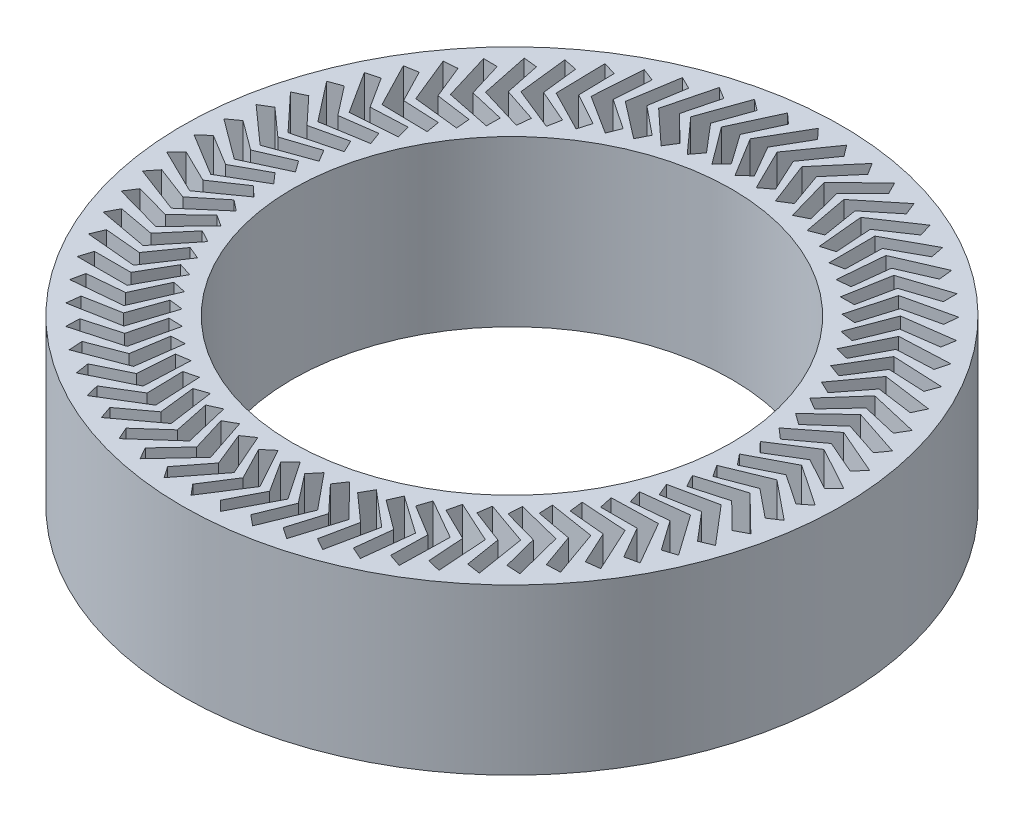
SolidWorks part; units mm, degrees
material "BUTYL"
ref_plane "Front Plane" through (0, 0, 0) normal (0, 0, 1) x (1, 0, 0)
ref_plane "Top Plane" through (0, 0, 0) normal (0, 1, 0) x (1, 0, 0)
ref_plane "Right Plane" through (0, 0, 0) normal (1, 0, 0) x (0, 0, -1)
sketch "Sketch1" plane through (0, 0, 0) normal (0, 1, 0) x (1, 0, 0)
  circle A0 centre (0, 0) radius 152.4
  circle A1 centre (0, 0) radius 101.6
  dimension "D1" = 304.8
  dimension "D2" = 203.2
extrude "Boss-Extrude1" add sketch "Sketch1" along normal blind 76.2
sketch "Sketch2" plane through (0, 76.2, 0) normal (0, 1, 0) x (1, 0, 0)
  line L0 (0, 0) -> (0, 152.4) construction
  line L1 (0, 141.3041) -> (-4.2887, 145.987)
  line L2 (-4.2887, 145.987) -> (-15.8221, 126.0106)
  line L3 (-15.8221, 126.0106) -> (-4.6829, 107.8484)
  line L4 (-4.6829, 107.8484) -> (0, 112.1371)
  line L5 (0, 141.3041) -> (-8.4198, 126.7206)
  line L6 (-8.4198, 126.7206) -> (0, 112.1371)
  line L7 (3.1384, 126.9612) -> (10.1972, 111.6725)
  line L8 (5.1437, 107.8274) -> (10.1972, 111.6725)
  line L9 (-4.2978, 126.9273) -> (5.1437, 107.8274)
  line L10 (9.0044, 145.7722) -> (-4.2978, 126.9273)
  line L11 (12.8495, 140.7187) -> (9.0044, 145.7722)
  line L12 (12.8495, 140.7187) -> (3.1384, 126.9612)
  line L13 (14.6706, 126.1498) -> (20.3098, 110.2825)
  line L14 (14.9276, 106.9129) -> (20.3098, 110.2825)
  line L15 (7.2621, 126.7922) -> (14.9276, 106.9129)
  line L16 (22.2229, 144.3494) -> (7.2621, 126.7922)
  line L17 (25.5925, 138.9672) -> (22.2229, 144.3494)
  line L18 (25.5925, 138.9672) -> (14.6706, 126.1498)
  line L19 (26.0812, 124.2931) -> (30.2542, 107.9787)
  line L20 (24.5879, 105.1125) -> (30.2542, 107.9787)
  line L21 (18.7619, 125.6065) -> (24.5879, 105.1125)
  line L22 (35.2572, 141.7305) -> (18.7619, 125.6065)
  line L23 (38.1234, 136.0642) -> (35.2572, 141.7305)
  line L24 (38.1234, 136.0642) -> (26.0812, 124.2931)
  line L25 (37.2757, 121.4064) -> (39.9479, 104.7802)
  line L26 (34.0444, 102.4411) -> (39.9479, 104.7802)
  line L27 (30.1061, 123.38) -> (34.0444, 102.4411)
  line L28 (47.9993, 137.9372) -> (30.1061, 123.38)
  line L29 (50.3384, 132.0337) -> (47.9993, 137.9372)
  line L30 (50.3384, 132.0337) -> (37.2757, 121.4064)
  line L31 (48.1614, 117.5137) -> (49.3106, 100.7134)
  line L32 (43.2188, 98.9209) -> (49.3106, 100.7134)
  line L33 (41.201, 120.1311) -> (43.2188, 98.9209)
  line L34 (60.3438, 133.0009) -> (41.201, 120.1311)
  line L35 (62.1363, 126.9091) -> (60.3438, 133.0009)
  line L36 (62.1363, 126.9091) -> (48.1614, 117.5137)
  line L37 (58.6479, 112.6473) -> (58.2646, 95.8121)
  line L38 (52.0351, 94.5809) -> (58.2646, 95.8121)
  line L39 (51.9544, 115.8868) -> (52.0351, 94.5809)
  line L40 (72.1882, 126.9625) -> (51.9544, 115.8868)
  line L41 (73.4193, 120.733) -> (72.1882, 126.9625)
  line L42 (73.4193, 120.733) -> (58.6479, 112.6473)
  line L43 (68.6485, 106.8475) -> (66.7359, 90.1168)
  line L44 (60.4202, 89.4572) -> (66.7359, 90.1168)
  line L45 (62.2772, 110.6822) -> (60.4202, 89.4572)
  line L46 (83.4344, 119.872) -> (62.2772, 110.6822)
  line L47 (84.094, 113.5564) -> (83.4344, 119.872)
  line L48 (84.094, 113.5564) -> (68.6485, 106.8475)
  line L49 (78.0803, 100.1622) -> (74.6541, 83.6748)
  line L50 (68.3047, 83.5923) -> (74.6541, 83.6748)
  line L51 (72.0841, 104.5604) -> (68.3047, 83.5923)
  line L52 (93.9893, 111.7883) -> (72.0841, 104.5604)
  line L53 (94.0718, 105.4388) -> (93.9893, 111.7883)
  line L54 (94.0718, 105.4388) -> (78.0803, 100.1622)
  line L55 (86.865, 92.647) -> (81.9538, 76.5395)
  line L56 (75.6231, 77.0347) -> (81.9538, 76.5395)
  line L57 (81.2936, 97.5723) -> (75.6231, 77.0347)
  line L58 (103.7653, 102.7782) -> (81.2936, 97.5723)
  line L59 (103.2701, 96.4476) -> (103.7653, 102.7782)
  line L60 (103.2701, 96.4476) -> (86.865, 92.647)
  line L61 (94.93, 84.3641) -> (88.5744, 68.7699)
  line L62 (82.315, 69.8387) -> (88.5744, 68.7699)
  line L63 (89.8295, 89.7756) -> (82.315, 69.8387)
  line L64 (112.6815, 92.9165) -> (89.8295, 89.7756)
  line L65 (111.6127, 86.6571) -> (112.6815, 92.9165)
  line L66 (111.6127, 86.6571) -> (94.93, 84.3641)
  line L67 (102.2083, 75.3821) -> (94.461, 60.4305)
  line L68 (88.3247, 62.0641) -> (94.461, 60.4305)
  line L69 (97.6211, 81.235) -> (88.3247, 62.0641)
  line L70 (120.664, 82.2849) -> (97.6211, 81.235)
  line L71 (119.0304, 76.1486) -> (120.664, 82.2849)
  line L72 (119.0304, 76.1486) -> (102.2083, 75.3821)
  line L73 (108.6397, 65.7755) -> (99.5648, 51.5903)
  line L74 (93.6025, 53.7752) -> (99.5648, 51.5903)
  line L75 (104.6037, 72.0213) -> (93.6025, 53.7752)
  line L76 (127.6466, 70.9714) -> (104.6037, 72.0213)
  line L77 (125.4618, 65.0091) -> (127.6466, 70.9714)
  line L78 (125.4618, 65.0091) -> (108.6397, 65.7755)
  line L79 (114.1709, 55.6239) -> (103.8437, 42.3227)
  line L80 (98.1048, 45.0406) -> (103.8437, 42.3227)
  line L81 (110.7196, 62.2107) -> (98.1048, 45.0406)
  line L82 (133.5716, 59.0698) -> (110.7196, 62.2107)
  line L83 (130.8536, 53.3309) -> (133.5716, 59.0698)
  line L84 (130.8536, 53.3309) -> (114.1709, 55.6239)
  line L85 (118.756, 45.0113) -> (107.2621, 32.7043)
  line L86 (101.7941, 35.9329) -> (107.2621, 32.7043)
  line L87 (115.918, 51.8847) -> (101.7941, 35.9329)
  line L88 (138.3897, 46.6788) -> (115.918, 51.8847)
  line L89 (135.1611, 41.2108) -> (138.3897, 46.6788)
  line L90 (135.1611, 41.2108) -> (118.756, 45.0113)
  line L91 (122.3571, 34.0258) -> (109.7916, 22.815)
  line L92 (104.6399, 26.5274) -> (109.7916, 22.815)
  line L93 (120.1558, 41.1288) -> (104.6399, 26.5274)
  line L94 (142.061, 33.9009) -> (120.1558, 41.1288)
  line L95 (138.3486, 28.7492) -> (142.061, 33.9009)
  line L96 (138.3486, 28.7492) -> (122.3571, 34.0258)
  line L97 (124.9442, 22.7583) -> (111.4114, 12.7365)
  line L98 (106.6186, 16.902) -> (111.4114, 12.7365)
  line L99 (123.398, 30.032) -> (106.6186, 16.902)
  line L100 (144.5552, 20.8422) -> (123.398, 30.032)
  line L101 (140.3897, 16.0493) -> (144.5552, 20.8422)
  line L102 (140.3897, 16.0493) -> (124.9442, 22.7583)
  line L103 (126.4961, 11.3022) -> (112.108, 2.5526)
  line L104 (107.7138, 7.1367) -> (112.108, 2.5526)
  line L105 (125.6177, 18.6864) -> (107.7138, 7.1367)
  line L106 (145.8516, 7.6107) -> (125.6177, 18.6864)
  line L107 (141.2675, 3.2165) -> (145.8516, 7.6107)
  line L108 (141.2675, 3.2165) -> (126.4961, 11.3022)
  line L109 (126.9998, -0.2475) -> (111.8756, -7.6525)
  line L110 (107.9165, -2.6878) -> (111.8756, -7.6525)
  line L111 (126.7965, 7.186) -> (107.9165, -2.6878)
  line L112 (145.9394, -5.6838) -> (126.7965, 7.186)
  line L113 (140.9747, -9.6429) -> (145.9394, -5.6838)
  line L114 (140.9747, -9.6429) -> (126.9998, -0.2475)
  line L115 (126.4511, -11.7952) -> (110.7163, -17.7942)
  line L116 (107.225, -12.4901) -> (110.7163, -17.7942)
  line L117 (126.9247, -4.374) -> (107.225, -12.4901)
  line L118 (144.8179, -18.9312) -> (126.9247, -4.374)
  line L119 (139.5137, -22.4225) -> (144.8179, -18.9312)
  line L120 (139.5137, -22.4225) -> (126.4511, -11.7952)
  line L121 (124.8546, -23.2452) -> (108.6394, -27.7884)
  line L122 (105.645, -22.1888) -> (108.6394, -27.7884)
  line L123 (126.001, -15.8978) -> (105.645, -22.1888)
  line L124 (142.4963, -32.0218) -> (126.001, -15.8978)
  line L125 (136.8967, -35.0163) -> (142.4963, -32.0218)
  line L126 (136.8967, -35.0163) -> (124.8546, -23.2452)
  line L127 (122.2235, -34.5025) -> (105.6624, -37.5524)
  line L128 (103.1895, -31.7037) -> (105.6624, -37.5524)
  line L129 (124.0333, -27.2898) -> (103.1895, -31.7037)
  line L130 (138.9941, -44.847) -> (124.0333, -27.2898)
  line L131 (133.1453, -47.3199) -> (138.9941, -44.847)
  line L132 (133.1453, -47.3199) -> (122.2235, -34.5025)
  line L133 (118.5796, -45.4739) -> (101.8098, -47.0052)
  line L134 (99.879, -40.9559) -> (101.8098, -47.0052)
  line L135 (121.0378, -38.4557) -> (99.879, -40.9559)
  line L136 (134.34, -57.3006) -> (121.0378, -38.4557)
  line L137 (128.2907, -59.2314) -> (134.34, -57.3006)
  line L138 (128.2907, -59.2314) -> (118.5796, -45.4739)
  line L139 (113.9531, -56.0685) -> (97.1135, -56.0685)
  line L140 (95.7409, -49.8687) -> (97.1135, -56.0685)
  line L141 (117.0394, -49.3029) -> (95.7409, -49.8687)
  line L142 (128.5728, -69.2794) -> (117.0394, -49.3029)
  line L143 (122.3729, -70.6521) -> (128.5728, -69.2794)
  line L144 (122.3729, -70.6521) -> (113.9531, -56.0685)
  line L145 (108.3824, -66.1985) -> (91.6126, -64.6672)
  line L146 (90.8094, -58.3682) -> (91.6126, -64.6672)
  line L147 (112.0711, -59.7416) -> (90.8094, -58.3682)
  line L148 (121.7402, -80.6841) -> (112.0711, -59.7416)
  line L149 (115.4412, -81.4873) -> (121.7402, -80.6841)
  line L150 (115.4412, -81.4873) -> (108.3824, -66.1985)
  line L151 (101.9136, -75.78) -> (85.3525, -72.7301)
  line L152 (85.1255, -66.3842) -> (85.3525, -72.7301)
  line L153 (106.1742, -69.6853) -> (85.1255, -66.3842)
  line L154 (113.8988, -91.4203) -> (106.1742, -69.6853)
  line L155 (107.5529, -91.6473) -> (113.8988, -91.4203)
  line L156 (107.5529, -91.6473) -> (101.9136, -75.78)
  line L157 (94.6003, -84.7336) -> (78.3852, -80.1903)
  line L158 (78.7362, -73.85) -> (78.3852, -80.1903)
  line L159 (99.3975, -79.0515) -> (78.7362, -73.85)
  line L160 (105.1136, -101.3989) -> (99.3975, -79.0515)
  line L161 (98.7733, -101.0479) -> (105.1136, -101.3989)
  line L162 (98.7733, -101.0479) -> (94.6003, -84.7336)
  line L163 (86.5032, -92.985) -> (70.7684, -86.986)
  line L164 (71.6944, -80.7039) -> (70.7684, -86.986)
  line L165 (91.7971, -87.7627) -> (71.6944, -80.7039)
  line L166 (95.4574, -110.5372) -> (91.7971, -87.7627)
  line L167 (89.1753, -109.6112) -> (95.4574, -110.5372)
  line L168 (89.1753, -109.6112) -> (86.5032, -92.985)
  line L169 (77.6892, -100.4659) -> (62.5651, -93.0609)
  line L170 (64.0586, -86.889) -> (62.5651, -93.0609)
  line L171 (83.4361, -95.7466) -> (64.0586, -86.889)
  line L172 (85.0102, -118.7597) -> (83.4361, -95.7466)
  line L173 (78.8384, -117.2662) -> (85.0102, -118.7597)
  line L174 (78.8384, -117.2662) -> (77.6892, -100.4659)
  line L175 (68.2315, -107.1143) -> (53.8434, -98.3647)
  line L176 (55.8919, -92.3542) -> (53.8434, -98.3647)
  line L177 (74.3837, -102.9372) -> (55.8919, -92.3542)
  line L178 (73.8586, -125.998) -> (74.3837, -102.9372)
  line L179 (67.8481, -123.9495) -> (73.8586, -125.998)
  line L180 (67.8481, -123.9495) -> (68.2315, -107.1143)
  line L181 (58.2084, -112.8751) -> (44.6755, -102.8534)
  line L182 (47.2621, -97.0541) -> (44.6755, -102.8534)
  line L183 (64.715, -109.2748) -> (47.2621, -97.0541)
  line L184 (62.095, -132.1923) -> (64.715, -109.2748)
  line L185 (56.2957, -129.6057) -> (62.095, -132.1923)
  line L186 (56.2957, -129.6057) -> (58.2084, -112.8751)
  line L187 (47.7029, -117.7006) -> (35.1375, -106.4898)
  line L188 (38.2407, -100.9497) -> (35.1375, -106.4898)
  line L189 (54.5099, -114.7069) -> (38.2407, -100.9497)
  line L190 (49.8169, -137.2912) -> (54.5099, -114.7069)
  line L191 (44.2768, -134.188) -> (49.8169, -137.2912)
  line L192 (44.2768, -134.188) -> (47.7029, -117.7006)
  line L193 (36.8022, -121.5508) -> (25.3083, -109.2438)
  line L194 (28.9024, -104.0089) -> (25.3083, -109.2438)
  line L195 (43.8532, -119.1885) -> (28.9024, -104.0089)
  line L196 (37.1259, -141.2525) -> (43.8532, -119.1885)
  line L197 (31.891, -137.6583) -> (37.1259, -141.2525)
  line L198 (31.891, -137.6583) -> (36.8022, -121.5508)
  line L199 (25.5965, -124.3938) -> (15.2693, -111.0926)
  line L200 (19.3246, -106.2062) -> (15.2693, -111.0926)
  line L201 (32.8332, -122.6824) -> (19.3246, -106.2062)
  line L202 (24.1273, -144.0433) -> (32.8332, -122.6824)
  line L203 (19.2409, -139.988) -> (24.1273, -144.0433)
  line L204 (19.2409, -139.988) -> (25.5965, -124.3938)
  line L205 (14.1787, -126.206) -> (5.1039, -112.0209)
  line L206 (9.5867, -107.5235) -> (5.1039, -112.0209)
  line L207 (21.541, -125.1598) -> (9.5867, -107.5235)
  line L208 (10.9288, -145.6405) -> (21.541, -125.1598)
  line L209 (6.4314, -141.1577) -> (10.9288, -145.6405)
  line L210 (6.4314, -141.1577) -> (14.1787, -126.206)
  line L211 (2.6434, -126.9725) -> (-5.1039, -112.0209)
  line L212 (-0.2306, -107.9498) -> (-5.1039, -112.0209)
  line L213 (10.0704, -126.6001) -> (-0.2306, -107.9498)
  line L214 (-2.3603, -146.0309) -> (10.0704, -126.6001)
  line L215 (-6.4314, -141.1577) -> (-2.3603, -146.0309)
  line L216 (-6.4314, -141.1577) -> (2.6434, -126.9725)
  line L217 (-8.9137, -126.6868) -> (-15.2693, -111.0926)
  line L218 (-10.0461, -107.4815) -> (-15.2693, -111.0926)
  line L219 (-1.4837, -126.9913) -> (-10.0461, -107.4815)
  line L220 (-15.6298, -145.2113) -> (-1.4837, -126.9913)
  line L221 (-19.2409, -139.988) -> (-15.6298, -145.2113)
  line L222 (-19.2409, -139.988) -> (-8.9137, -126.6868)
  line L223 (-20.3971, -125.3513) -> (-25.3083, -109.2438)
  line L224 (-19.7783, -106.1227) -> (-25.3083, -109.2438)
  line L225 (-13.0255, -126.3303) -> (-19.7783, -106.1227)
  line L226 (-28.7698, -143.1883) -> (-13.0255, -126.3303)
  line L227 (-31.891, -137.6583) -> (-28.7698, -143.1883)
  line L228 (-31.891, -137.6583) -> (-20.3971, -125.3513)
  line L229 (-31.7114, -122.9772) -> (-35.1375, -106.4898)
  line L230 (-29.3466, -103.8845) -> (-35.1375, -106.4898)
  line L231 (-24.4594, -124.6224) -> (-29.3466, -103.8845)
  line L232 (-41.6714, -139.9789) -> (-24.4594, -124.6224)
  line L233 (-44.2768, -134.188) -> (-41.6714, -139.9789)
  line L234 (-44.2768, -134.188) -> (-31.7114, -122.9772)
  line L235 (-42.7629, -119.584) -> (-44.6755, -102.8534)
  line L236 (-38.6717, -100.7854) -> (-44.6755, -102.8534)
  line L237 (-35.6905, -121.8819) -> (-38.6717, -100.7854)
  line L238 (-54.2278, -135.6096) -> (-35.6905, -121.8819)
  line L239 (-56.2957, -129.6057) -> (-54.2278, -135.6096)
  line L240 (-56.2957, -129.6057) -> (-42.7629, -119.584)
  line L241 (-53.4601, -115.1999) -> (-53.8434, -98.3647)
  line L242 (-47.6764, -96.8513) -> (-53.8434, -98.3647)
  line L243 (-46.626, -118.1314) -> (-47.6764, -96.8513)
  line L244 (-66.3347, -130.1165) -> (-46.626, -118.1314)
  line L245 (-67.8481, -123.9495) -> (-66.3347, -130.1165)
  line L246 (-67.8481, -123.9495) -> (-53.4601, -115.1999)
  line L247 (-63.7143, -109.8612) -> (-62.5651, -93.0609)
  line L248 (-56.286, -92.1145) -> (-62.5651, -93.0609)
  line L249 (-57.1751, -113.402) -> (-56.286, -92.1145)
  line L250 (-77.892, -123.5453) -> (-57.1751, -113.402)
  line L251 (-78.8384, -117.2662) -> (-77.892, -123.5453)
  line L252 (-78.8384, -117.2662) -> (-63.7143, -109.8612)
  line L253 (-73.4405, -103.6122) -> (-70.7684, -86.986)
  line L254 (-64.4292, -86.6145) -> (-70.7684, -86.986)
  line L255 (-67.2504, -107.733) -> (-64.4292, -86.6145)
  line L256 (-88.8039, -115.9503) -> (-67.2504, -107.733)
  line L257 (-89.1753, -109.6112) -> (-88.8039, -115.9503)
  line L258 (-89.1753, -109.6112) -> (-73.4405, -103.6122)
  line L259 (-82.5582, -96.5046) -> (-78.3852, -80.1903)
  line L260 (-72.0386, -80.3968) -> (-78.3852, -80.1903)
  line L261 (-76.7684, -101.1712) -> (-72.0386, -80.3968)
  line L262 (-98.9799, -107.3945) -> (-76.7684, -101.1712)
  line L263 (-98.7733, -101.0479) -> (-98.9799, -107.3945)
  line L264 (-98.7733, -101.0479) -> (-82.5582, -96.5046)
  line L265 (-90.9918, -88.5974) -> (-85.3525, -72.7301)
  line L266 (-79.051, -73.5129) -> (-85.3525, -72.7301)
  line L267 (-85.6503, -93.7711) -> (-79.051, -73.5129)
  line L268 (-108.3357, -97.9489) -> (-85.6503, -93.7711)
  line L269 (-107.5529, -91.6473) -> (-108.3357, -97.9489)
  line L270 (-107.5529, -91.6473) -> (-90.9918, -88.5974)
  line L271 (-98.6714, -79.956) -> (-91.6126, -64.6672)
  line L272 (-85.4083, -66.0198) -> (-91.6126, -64.6672)
  line L273 (-93.8225, -85.594) -> (-85.4083, -66.0198)
  line L274 (-116.7938, -87.6916) -> (-93.8225, -85.594)
  line L275 (-115.4412, -81.4873) -> (-116.7938, -87.6916)
  line L276 (-115.4412, -81.4873) -> (-98.6714, -79.956)
  line L277 (-105.5333, -70.6521) -> (-97.1135, -56.0685)
  line L278 (-91.058, -57.9797) -> (-97.1135, -56.0685)
  line L279 (-101.2173, -76.7076) -> (-91.058, -57.9797)
  line L280 (-124.2841, -76.7076) -> (-101.2173, -76.7076)
  line L281 (-122.3729, -70.6521) -> (-124.2841, -76.7076)
  line L282 (-122.3729, -70.6521) -> (-105.5333, -70.6521)
  line L283 (-111.5208, -60.7627) -> (-101.8098, -47.0052)
  line L284 (-95.9531, -49.4591) -> (-101.8098, -47.0052)
  line L285 (-107.7733, -67.1856) -> (-95.9531, -49.4591)
  line L286 (-130.7446, -65.088) -> (-107.7733, -67.1856)
  line L287 (-128.2907, -59.2314) -> (-130.7446, -65.088)
  line L288 (-128.2907, -59.2314) -> (-111.5208, -60.7627)
  line L289 (-116.5842, -50.3698) -> (-105.6624, -37.5524)
  line L290 (-100.0531, -40.5287) -> (-105.6624, -37.5524)
  line L291 (-113.4363, -57.1069) -> (-100.0531, -40.5287)
  line L292 (-136.1217, -52.9291) -> (-113.4363, -57.1069)
  line L293 (-133.1453, -47.3199) -> (-136.1217, -52.9291)
  line L294 (-133.1453, -47.3199) -> (-116.5842, -50.3698)
  line L295 (-120.6816, -39.5595) -> (-108.6394, -27.7884)
  line L296 (-103.324, -31.2625) -> (-108.6394, -27.7884)
  line L297 (-118.1594, -46.555) -> (-103.324, -31.2625)
  line L298 (-140.3708, -40.3316) -> (-118.1594, -46.555)
  line L299 (-136.8967, -35.0163) -> (-140.3708, -40.3316)
  line L300 (-136.8967, -35.0163) -> (-120.6816, -39.5595)
  line L301 (-123.7789, -28.4215) -> (-110.7163, -17.7942)
  line L302 (-105.7388, -21.7372) -> (-110.7163, -17.7942)
  line L303 (-121.9033, -35.6173) -> (-105.7388, -21.7372)
  line L304 (-143.4568, -27.3999) -> (-121.9033, -35.6173)
  line L305 (-139.5137, -22.4225) -> (-143.4568, -27.3999)
  line L306 (-139.5137, -22.4225) -> (-123.7789, -28.4215)
  line L307 (-125.8506, -17.0479) -> (-111.8756, -7.6525)
  line L308 (-107.2774, -12.0318) -> (-111.8756, -7.6525)
  line L309 (-124.6371, -24.3845) -> (-107.2774, -12.0318)
  line L310 (-145.354, -14.2412) -> (-124.6371, -24.3845)
  line L311 (-140.9747, -9.6429) -> (-145.354, -14.2412)
  line L312 (-140.9747, -9.6429) -> (-125.8506, -17.0479)
  line L313 (-126.8794, -5.5331) -> (-112.108, 2.5526)
  line L314 (-107.927, -2.2267) -> (-112.108, 2.5526)
  line L315 (-126.3381, -12.9496) -> (-107.927, -2.2267)
  line L316 (-146.0468, -0.9644) -> (-126.3381, -12.9496)
  line L317 (-141.2675, 3.2165) -> (-146.0468, -0.9644)
  line L318 (-141.2675, 3.2165) -> (-126.8794, -5.5331)
  line L319 (-126.8569, 6.0276) -> (-111.4114, 12.7365)
  line L320 (-107.6824, 7.5968) -> (-111.4114, 12.7365)
  line L321 (-126.9922, -1.4074) -> (-107.6824, 7.5968)
  line L322 (-145.5294, 12.3203) -> (-126.9922, -1.4074)
  line L323 (-140.3897, 16.0493) -> (-145.5294, 12.3203)
  line L324 (-140.3897, 16.0493) -> (-126.8569, 6.0276)
  line L325 (-125.7832, 17.5384) -> (-109.7916, 22.815)
  line L326 (-106.5454, 17.3574) -> (-109.7916, 22.815)
  line L327 (-126.594, 10.1464) -> (-106.5454, 17.3574)
  line L328 (-143.8061, 25.503) -> (-126.594, 10.1464)
  line L329 (-138.3486, 28.7492) -> (-143.8061, 25.503)
  line L330 (-138.3486, 28.7492) -> (-125.7832, 17.5384)
  line L331 (-123.6672, 28.9038) -> (-107.2621, 32.7043)
  line L332 (-104.5256, 26.9742) -> (-107.2621, 32.7043)
  line L333 (-125.1469, 21.6162) -> (-104.5256, 26.9742)
  line L334 (-140.8912, 38.4743) -> (-125.1469, 21.6162)
  line L335 (-135.1611, 41.2108) -> (-140.8912, 38.4743)
  line L336 (-135.1611, 41.2108) -> (-123.6672, 28.9038)
  line L337 (-120.5264, 40.0297) -> (-103.8437, 42.3227)
  line L338 (-101.6396, 36.3675) -> (-103.8437, 42.3227)
  line L339 (-122.6627, 32.9069) -> (-101.6396, 36.3675)
  line L340 (-136.8088, 51.1268) -> (-122.6627, 32.9069)
  line L341 (-130.8536, 53.3309) -> (-136.8088, 51.1268)
  line L342 (-130.8536, 53.3309) -> (-120.5264, 40.0297)
  line L343 (-116.387, 50.8239) -> (-99.5648, 51.5903)
  line L344 (-97.9114, 45.4594) -> (-99.5648, 51.5903)
  line L345 (-119.1621, 43.9248) -> (-97.9114, 45.4594)
  line L346 (-131.5928, 63.3557) -> (-119.1621, 43.9248)
  line L347 (-125.4618, 65.0091) -> (-131.5928, 63.3557)
  line L348 (-125.4618, 65.0091) -> (-116.387, 50.8239)
  line L349 (-111.2831, 61.197) -> (-94.461, 60.4305)
  line L350 (-93.3719, 54.1746) -> (-94.461, 60.4305)
  line L351 (-114.6741, 54.5788) -> (-93.3719, 54.1746)
  line L352 (-125.2863, 75.0595) -> (-114.6741, 54.5788)
  line L353 (-119.0304, 76.1486) -> (-125.2863, 75.0595)
  line L354 (-119.0304, 76.1486) -> (-111.2831, 61.197)
  line L355 (-105.2571, 71.0629) -> (-88.5744, 68.7699)
  line L356 (-88.0587, 62.4409) -> (-88.5744, 68.7699)
  line L357 (-109.2359, 64.7806) -> (-88.0587, 62.4409)
  line L358 (-117.9417, 86.1415) -> (-109.2359, 64.7806)
  line L359 (-111.6127, 86.6571) -> (-117.9417, 86.1415)
  line L360 (-111.6127, 86.6571) -> (-105.2571, 71.0629)
  line L361 (-98.3589, 80.34) -> (-81.9538, 76.5395)
  line L362 (-82.0158, 70.1898) -> (-81.9538, 76.5395)
  line L363 (-102.8925, 74.4455) -> (-82.0158, 70.1898)
  line L364 (-109.6198, 96.5096) -> (-102.8925, 74.4455)
  line L365 (-103.2701, 96.4476) -> (-109.6198, 96.5096)
  line L366 (-103.2701, 96.4476) -> (-98.3589, 80.34)
  line L367 (-90.6457, 88.9514) -> (-74.6541, 83.6748)
  line L368 (-75.2933, 77.3571) -> (-74.6541, 83.6748)
  line L369 (-95.6965, 83.4936) -> (-75.2933, 77.3571)
  line L370 (-100.3896, 106.078) -> (-95.6965, 83.4936)
  line L371 (-94.0718, 105.4388) -> (-100.3896, 106.078)
  line L372 (-94.0718, 105.4388) -> (-90.6457, 88.9514)
  line L373 (-82.1813, 96.8257) -> (-66.7359, 90.1168)
  line L374 (-67.9469, 83.8834) -> (-66.7359, 90.1168)
  line L375 (-87.7075, 91.8498) -> (-67.9469, 83.8834)
  line L376 (-90.3274, 114.7674) -> (-87.7075, 91.8498)
  line L377 (-84.094, 113.5564) -> (-90.3274, 114.7674)
  line L378 (-84.094, 113.5564) -> (-82.1813, 96.8257)
  line L379 (-73.036, 103.8977) -> (-58.2646, 95.8121)
  line L380 (-60.0375, 89.7146) -> (-58.2646, 95.8121)
  line L381 (-78.9918, 99.445) -> (-60.0375, 89.7146)
  line L382 (-79.5168, 122.5058) -> (-78.9918, 99.445)
  line L383 (-73.4193, 120.733) -> (-79.5168, 122.5058)
  line L384 (-73.4193, 120.733) -> (-73.036, 103.8977)
  line L385 (-63.2855, 110.1088) -> (-49.3106, 100.7134)
  line L386 (-51.6305, 94.8024) -> (-49.3106, 100.7134)
  line L387 (-69.6215, 106.216) -> (-51.6305, 94.8024)
  line L388 (-68.0473, 129.2291) -> (-69.6215, 106.216)
  line L389 (-62.1363, 126.9091) -> (-68.0473, 129.2291)
  line L390 (-62.1363, 126.9091) -> (-63.2855, 110.1088)
  line L391 (-53.0106, 115.4075) -> (-39.9479, 104.7802)
  line L392 (-42.7958, 99.1046) -> (-39.9479, 104.7802)
  line L393 (-59.6743, 112.107) -> (-42.7958, 99.1046)
  line L394 (-56.014, 134.8816) -> (-59.6743, 112.107)
  line L395 (-50.3384, 132.0337) -> (-56.014, 134.8816)
  line L396 (-50.3384, 132.0337) -> (-53.0106, 115.4075)
  line L397 (-42.2964, 119.7498) -> (-30.2542, 107.9787)
  line L398 (-33.6064, 102.5856) -> (-30.2542, 107.9787)
  line L399 (-49.2326, 117.069) -> (-33.6064, 102.5856)
  line L400 (-43.5165, 139.4164) -> (-49.2326, 117.069)
  line L401 (-38.1234, 136.0642) -> (-43.5165, 139.4164)
  line L402 (-38.1234, 136.0642) -> (-42.2964, 119.7498)
  line L403 (-31.2317, 123.0999) -> (-20.3098, 110.2825)
  line L404 (-24.1386, 105.2166) -> (-20.3098, 110.2825)
  line L405 (-38.383, 121.0609) -> (-24.1386, 105.2166)
  line L406 (-30.6584, 142.7959) -> (-38.383, 121.0609)
  line L407 (-25.5925, 138.9672) -> (-30.6584, 142.7959)
  line L408 (-25.5925, 138.9672) -> (-31.2317, 123.0999)
  line L409 (-19.9082, 125.4299) -> (-10.1972, 111.6725)
  line L410 (-14.4707, 106.9757) -> (-10.1972, 111.6725)
  line L411 (-27.2153, 124.0497) -> (-14.4707, 106.9757)
  line L412 (-17.5462, 144.9922) -> (-27.2153, 124.0497)
  line L413 (-12.8495, 140.7187) -> (-17.5462, 144.9922)
  line L414 (-12.8495, 140.7187) -> (-19.9082, 125.4299)
  circle A0 centre (0, 0) radius 152.4 construction
  circle A1 centre (0, 0) radius 146.05 construction
  circle A2 centre (0, 0) radius 107.95 construction
  circle A3 centre (0, 0) radius 101.6 construction
  circle A4 centre (0, 0) radius 127 construction
  point P428 (0, 0)
  dimension "D1" = 6.35
  dimension "D2" = 6.35
  dimension "D5" = 25.4
  dimension "D3" = 6.35
  dimension "D4" = 30
  dimension "D7" = 106.9129
  dimension "D8" = 14.9276
  dimension "D6" = 69
extrude "Cut-Extrude2" cut sketch "Sketch2" against normal through all
